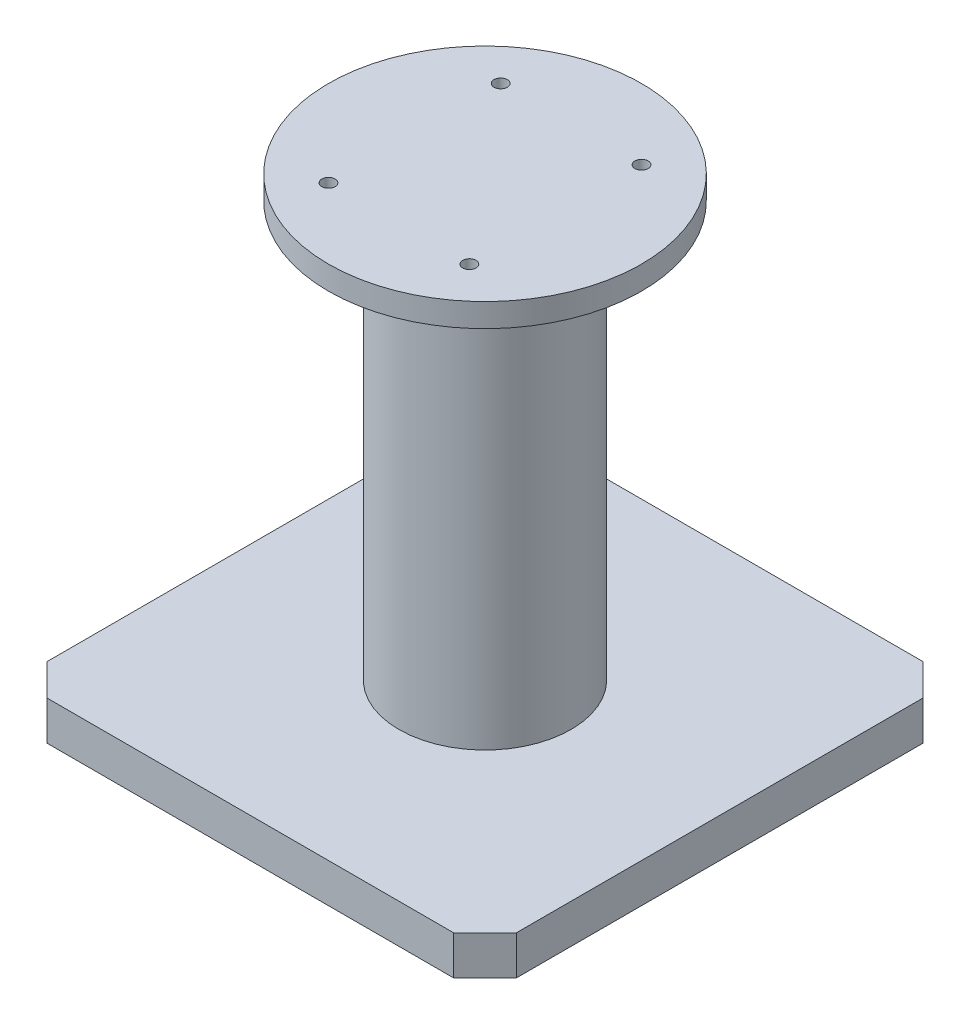
SolidWorks part; units mm, degrees
ref_plane "Front Plane" through (0, 0, 0) normal (0, 0, 1) x (1, 0, 0)
ref_plane "Top Plane" through (0, 0, 0) normal (0, 1, 0) x (1, 0, 0)
ref_plane "Right Plane" through (0, 0, 0) normal (1, 0, 0) x (0, 0, -1)
sketch "Sketch1" plane through (0, 0, 0) normal (0, 1, 0) x (1, 0, 0)
  line L5 (-150, 130) -> (-130, 150)
  line L6 (-130, -150) -> (130, -150)
  line L10 (-150, -130) -> (-150, 130)
  line L11 (-130, 150) -> (130, 150)
  line L12 (150, -130) -> (150, 130)
  line L13 (0, 150) -> (0, -150) construction
  line L14 (-150, 0) -> (150, 0) construction
  line L15 (-150, -130) -> (-130, -150)
  line L16 (130, -150) -> (150, -130)
  line L17 (150, 130) -> (130, 150)
  point P0 (0, 0)
  point P1 (150, 150)
  point P2 (-150, -150)
  point P3 (-150, 150)
  point P45 (150, -150)
  dimension "D1" = 300
  dimension "D2" = 300
  dimension "D3" = 150
  dimension "D4" = 150
extrude "Boss-Extrude1" add sketch "Sketch1" along normal blind 25
sketch "Sketch2" plane through (0, 25, 0) normal (0, 1, 0) x (1, 0, 0)
  circle A0 centre (0, 0) radius 55
  dimension "D1" = 110
extrude "Boss-Extrude2" add sketch "Sketch2" along normal blind 265
sketch "Sketch3" plane through (0, 290, 0) normal (0, 1, 0) x (1, 0, 0)
  circle A0 centre (0, 0) radius 100
  dimension "D1" = 200
extrude "Boss-Extrude3" add sketch "Sketch3" along normal blind 15
sketch "Sketch4" plane through (0, 305, 0) normal (0, 1, 0) x (1, 0, 0)
  line L0 (0, 0) -> (0, 100) construction
  line L1 (0, 0) -> (-71.0634, 0) construction
  circle A0 centre (0, 0) radius 71.0634
  circle A1 centre (-45, 55) radius 4.25
  circle A2 centre (0, 0) radius 100 construction
  circle A3 centre (45, 55) radius 4.25
  circle A4 centre (45, -55) radius 4.25
  circle A5 centre (-45, -55) radius 4.25
  point P16 (0, 0)
  dimension "D1" = 8.5
  dimension "D2" = 45
  dimension "D3" = 45
extrude "Cut-Extrude1" cut sketch "Sketch4" against normal blind 15 contours A0 A4 | A0 A4 | A1 | A5 | A3
